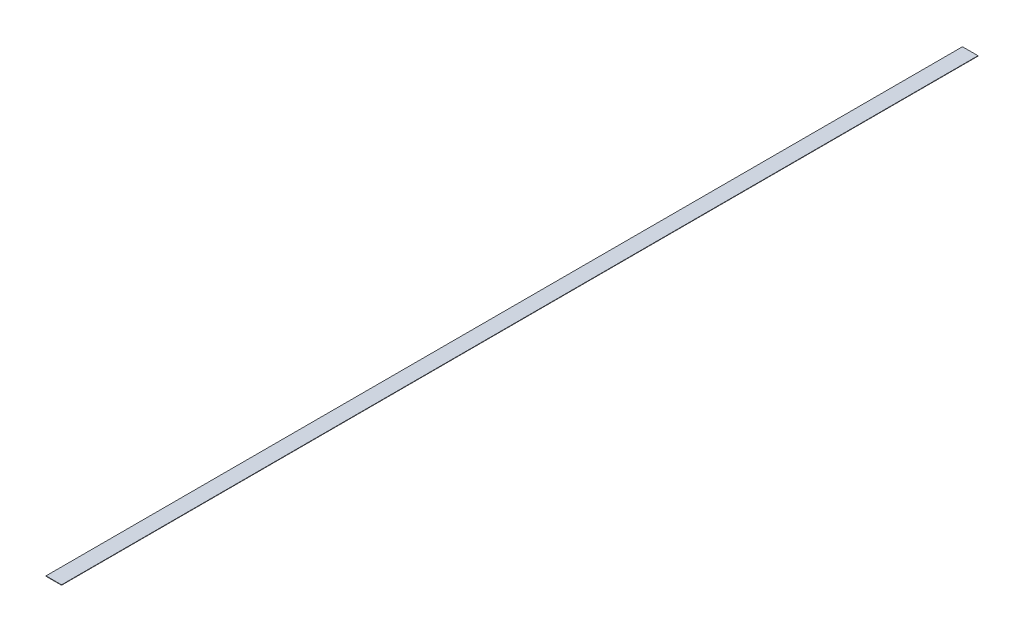
SolidWorks part; units mm, degrees
ref_plane "Front Plane" through (0, 0, 0) normal (0, 0, 1) x (1, 0, 0)
ref_plane "Top Plane" through (0, 0, 0) normal (0, 1, 0) x (1, 0, 0)
ref_plane "Right Plane" through (0, 0, 0) normal (1, 0, 0) x (0, 0, -1)
sketch "Sketch1" plane through (0, 0, 0) normal (0, 1, 0) x (1, 0, 0)
  line L1 (-25.4, 0) -> (25.4, 0)
  line L2 (-25.4, 0) -> (-25.4, 2997.2)
  line L3 (-25.4, 2997.2) -> (25.4, 2997.2)
  line L4 (25.4, 0) -> (25.4, 2997.2)
  dimension "D1" = 50.8
  dimension "D2" = 2997.2
extrude "Boss-Extrude1" add sketch "Sketch1" along normal blind 1.27
